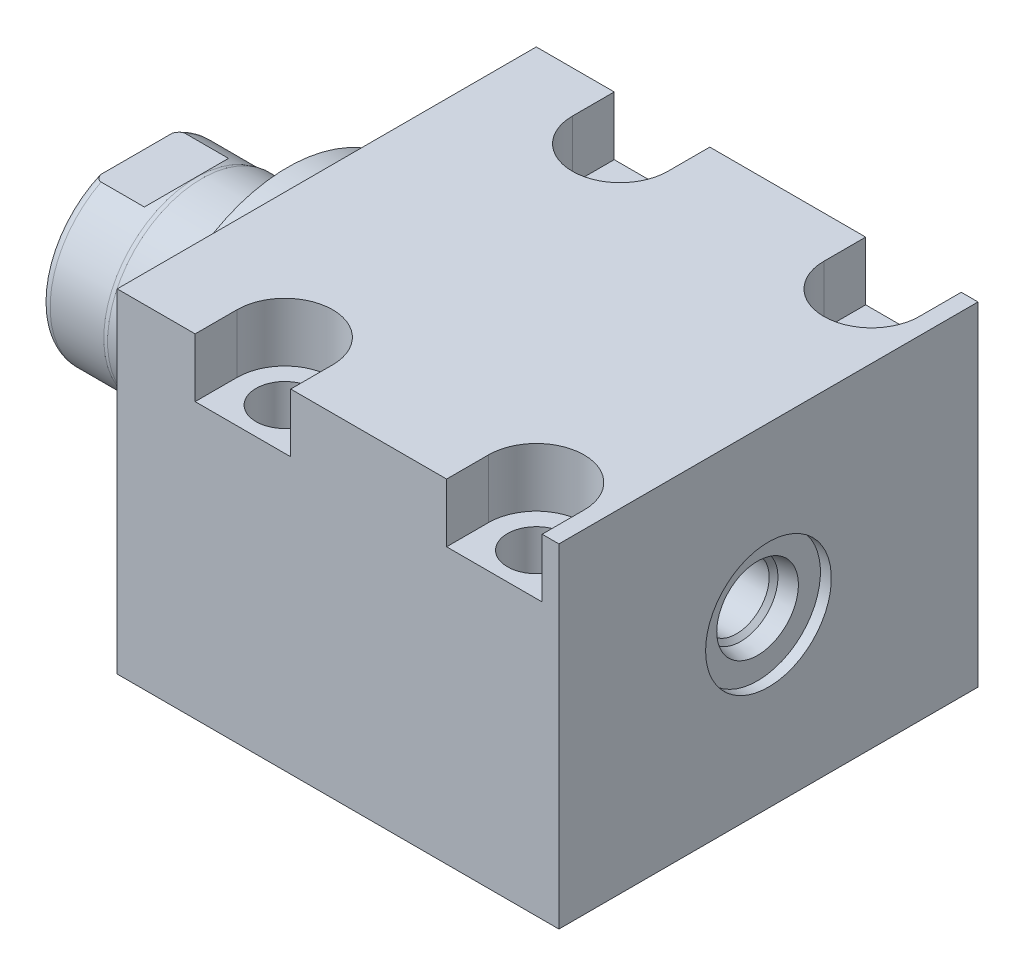
SolidWorks part; units mm, degrees
material "Alloy Steel"
ref_plane "Front Plane" through (0, 0, 0) normal (0, 0, 1) x (1, 0, 0)
ref_plane "Top Plane" through (0, 0, 0) normal (0, 1, 0) x (1, 0, 0)
ref_plane "Right Plane" through (0, 0, 0) normal (1, 0, 0) x (0, 0, -1)
ref_plane "Plane1" through (0, 0, 0) normal (1, 0, 0) x (0, 0, -1)
sketch "Sketch1" plane through (0, 0, 0) normal (1, 0, 0) x (0, 0, -1)
  line L0 (-31.75, 25.146) -> (31.75, 25.146)
  line L1 (31.75, 25.146) -> (31.75, -25.4)
  line L2 (31.75, -25.4) -> (-31.75, -25.4)
  line L3 (-31.75, -25.4) -> (-31.75, 25.146)
  line L4 (0, -24.4475) -> (0, 24.4475) construction
  dimension "D1" = 50.546
  dimension "D2" = 25.4
  dimension "D3" = 63.5
  dimension "D4" = 31.75
extrude "Extrude1" add sketch "Sketch1" along normal blind 66.929
sketch "Sketch5" plane through (0, 0, 0) normal (-1, 0, 0) x (0, 0, 1)
  circle A0 centre (0, 0) radius 22.225
  dimension "D1" = 44.45
extrude "Extrude2" add sketch "Sketch5" along normal blind 5.969
ref_plane "Plane5" through (0, 0, 0) normal (0, -1, 0) x (0, 0, 1)
sketch "Sketch6" plane through (0, 0, 0) normal (0, -1, 0) x (0, 0, 1)
  line L0 (0, 5.969) -> (-14.2875, 5.969)
  line L1 (-14.2875, 5.969) -> (-14.2875, 28.829)
  line L2 (-14.2875, 28.829) -> (0, 28.829)
  line L3 (0, 28.829) -> (0, 5.969)
  line L4 (0, -5.7546) -> (0, 21.1709) construction
  line L5 (22.225, 5.969) -> (-22.225, 5.969) construction
  line L6 (31.75, -66.929) -> (-31.75, -66.929) construction
  dimension "D1" = 95.758
  dimension "D2" = 28.575
revolve "Revolve1" add sketch "Sketch6" angle 360 about L4
ref_plane "Plane6" through (-18.5113, 3.2639, 0) normal (0, 0, 1) x (0, 1, 0)
sketch "S2D0001" plane through (-18.5113, 3.2639, 0) normal (0, 0, 1) x (0, 1, 0)
  line L0 (2.286, 8.25) -> (2.286, -6.5225)
  line L2 (3.4798, 10.3177) -> (-3.2639, 10.3177)
  line L3 (-3.2639, 10.3177) -> (-3.2639, -6.5225)
  line L4 (2.286, 8.25) -> (3.4798, 10.3177)
  line L5 (-3.2639, -18.5113) -> (-3.2639, 2.765) construction
  line L6 (11.0236, 10.3177) -> (-17.5514, 10.3177) construction
  line L7 (2.286, -6.5225) -> (-3.2639, -6.5225)
  dimension "D1" = 30
  dimension "D2" = 13.4874
  dimension "D3" = 11.0998
  dimension "D4" = 16.8402
revolve "Cut-Revolve4" cut sketch "S2D0001" angle 360 about L5
ref_plane "Plane7" through (0, 0, 0) normal (0, 1, 0) x (0, 0, -1)
sketch "Sketch8" plane through (0, 0, 0) normal (0, 1, 0) x (0, 0, -1)
  line L0 (-14.2875, 18.923) -> (-14.097, 19.685)
  line L1 (-14.097, 19.685) -> (-14.097, 27.813)
  line L2 (0, 12.6594) -> (0, 20.8178) construction
  line L3 (-14.2875, 18.923) -> (-14.2875, 28.829)
  line L4 (-13.7089, 28.829) -> (-14.2875, 28.829)
  line L5 (14.2875, 28.829) -> (-14.2875, 28.829) construction
  line L6 (-14.2875, 28.829) -> (-14.2875, 5.969) construction
  arc A0 (-13.7089, 28.829) -> (-14.097, 27.813) centre (-12.573, 27.813) ccw
  dimension "D2" = 1.524
  dimension "D1" = 28.194
  dimension "D3" = 1.016
  dimension "D4" = 0.762
  dimension "D5" = 9.144
revolve "Cut-Revolve5" cut sketch "Sketch8" angle 360 about L2
ref_plane "Plane11" through (0, 0, 0) normal (0, 0, -1) x (0, -1, 0)
sketch "Sketch12" plane through (0, 0, 0) normal (0, 0, -1) x (0, -1, 0)
  line L0 (12.573, 28.829) -> (12.573, 21.2598)
  line L1 (12.573, 21.2598) -> (14.097, 19.7358)
  line L2 (-12.573, 28.829) -> (-12.573, 21.2598)
  line L3 (-12.573, 21.2598) -> (-14.097, 19.7358)
  line L4 (12.573, 28.829) -> (14.097, 28.829)
  line L5 (0, 13.7262) -> (0, 20.767) construction
  line L6 (-14.097, 19.7358) -> (-14.097, 28.829)
  line L8 (14.097, 19.685) -> (14.097, 27.813) construction
  line L9 (14.097, 19.7358) -> (14.097, 28.829)
  line L10 (-12.573, 28.829) -> (-14.097, 28.829)
  line L12 (13.7089, 28.829) -> (-13.7089, 28.829) construction
  dimension "D1" = 25.146
  dimension "D2" = 7.5692
  dimension "D3" = 45
extrude "Cut-Extrude4" cut sketch "Sketch12" against normal mid plane 60.96
hole_wizard "Hole2" positions "Sketch17" profile "Sketch16" legacy
sketch "Sketch17" plane through (0, 25.146, 0) normal (0, 1, 0) x (-1, 0, 0)
  line L0 (0, 0) -> (-59.3363, 0) construction
  line L1 (0, -31.75) -> (0, 31.75) construction
  point P0 (-19.05, -25.4)
  point P9 (-19.05, 25.4)
  dimension "D1" = 50.8
  dimension "D2" = 19.05
sketch "Sketch16" plane through (19.05, 25.146, -25.4) normal (1, 0, 0) x (0, 0, 1)
  line L0 (0, 0) -> (0, 50.546)
  line L1 (0, 50.546) -> (4.3688, 50.546)
  line L2 (4.3688, 50.546) -> (4.3688, 0)
  line L3 (4.3688, 0) -> (0, 0)
  line L4 (0, 110) -> (0, -10) construction
  dimension "Diameter" = 8.7376
  dimension "Depth" = 50.546
pattern_linear "LPattern1" count 2 spacing 38.1 along (1, 0, 0) of "Hole2"
sketch "Sketch18" plane through (0, 25.146, 0) normal (0, 1, 0) x (1, 0, 0)
  line L0 (0, 0) -> (50.053, 0) construction
  line L2 (66.929, -31.75) -> (0, -31.75) construction
  line L4 (64.389, -31.75) -> (49.911, -31.75)
  line L5 (11.811, -25.4) -> (11.811, -31.75)
  line L6 (26.289, -25.4) -> (26.289, -31.75)
  line L7 (49.911, -25.4) -> (49.911, -31.75)
  line L8 (64.389, 25.4) -> (64.389, 31.75)
  line L9 (26.289, -31.75) -> (11.811, -31.75)
  line L12 (26.289, 31.75) -> (11.811, 31.75)
  line L14 (49.911, 25.4) -> (49.911, 31.75)
  line L15 (26.289, 25.4) -> (26.289, 31.75)
  line L16 (11.811, 25.4) -> (11.811, 31.75)
  line L17 (64.389, 31.75) -> (49.911, 31.75)
  line L18 (64.389, -25.4) -> (64.389, -31.75)
  arc A0 (26.289, -25.4) -> (11.811, -25.4) centre (19.05, -25.4) ccw
  arc A1 (64.389, -25.4) -> (49.911, -25.4) centre (57.15, -25.4) ccw
  arc A2 (64.389, 25.4) -> (49.911, 25.4) centre (57.15, 25.4) cw
  arc A3 (26.289, 25.4) -> (11.811, 25.4) centre (19.05, 25.4) cw
  dimension "D1" = 14.478
extrude "Cut-Extrude5" cut sketch "Sketch18" against normal blind 8.89
hole_wizard "Hole3" positions "Sketch20" profile "Sketch19" legacy
sketch "Sketch20" plane through (0, -25.4, 0) normal (0, -1, 0) x (1, 0, 0)
  line L0 (0, 31.75) -> (0, -31.75) construction
  point P0 (12.7, 0)
  dimension "D1" = 12.7
sketch "Sketch19" plane through (12.7, -25.4, 0) normal (1, 0, 0) x (0, 0, -1)
  line L0 (0, 0) -> (0, 10.4789)
  line L1 (0, 10.4789) -> (1.5875, 9.525)
  line L2 (1.5875, 9.525) -> (1.5875, 1.4478)
  line L3 (1.5875, 1.4478) -> (5.6705, 1.4478)
  line L4 (5.6705, 0) -> (0, 0)
  line L5 (0, -11.3109) -> (0, 121.1557) construction
  line L6 (0, 10.4789) -> (-1.5875, 9.525) construction
  line L7 (5.6705, 1.4478) -> (5.6705, 0)
  dimension "Depth" = 9.525
  dimension "Drill Angle" = 118
  dimension "Diameter" = 3.175
  dimension "C-Bore Diameter" = 11.3411
  dimension "C-Bore Depth" = 1.4478
hole_wizard "Hole4" positions "Sketch21" profile "Sketch22" legacy
sketch "Sketch21" plane through (0, -25.4, 0) normal (0, -1, 0) x (1, 0, 0)
  point P0 (50.8, 0)
  dimension "D1" = 38.1
sketch "Sketch22" plane through (50.8, -25.4, 0) normal (1, 0, 0) x (0, 0, -1)
  line L0 (0, 0) -> (0, 10.4789)
  line L1 (0, 10.4789) -> (1.5875, 9.525)
  line L2 (1.5875, 9.525) -> (1.5875, 1.4478)
  line L3 (1.5875, 1.4478) -> (5.6705, 1.4478)
  line L4 (5.6705, 0) -> (0, 0)
  line L5 (0, -11.3109) -> (0, 121.1557) construction
  line L6 (0, 10.4789) -> (-1.5875, 9.525) construction
  line L7 (5.6705, 1.4478) -> (5.6705, 0)
  dimension "Depth" = 9.525
  dimension "Drill Angle" = 118
  dimension "Diameter" = 3.175
  dimension "C-Bore Diameter" = 11.3411
  dimension "C-Bore Depth" = 1.4478
chamfer "Chamfer1" distance 0.635 angle 45 2 edges at (50.8, -23.9522, -1.5875) (12.7, -23.9522, -1.5875)
sketch "Sketch23" plane through (0, 0, 0) normal (0, 0, 1) x (1, 0, 0)
  line L0 (12.7, -23.9522) -> (12.7, -21.4272) construction
  line L1 (10.4775, -23.9522) -> (14.9225, -23.9522) construction
  line L2 (7.0294, -23.9522) -> (18.3705, -23.9522) construction
  line L3 (7.0294, -23.9522) -> (7.0294, -25.4) construction
  circle A0 centre (8.4772, -25.4) radius 1.4478
  dimension "D1" = 2.8956
revolve "Revolve2" add sketch "Sketch23" angle 360 about L0
pattern_linear "LPattern3" count 2 spacing 38.1 along (1, 0, 0) of bodies 128
sketch "Sketch24" plane through (0, 0, 0) normal (0, 0, 1) x (1, 0, 0)
  line L0 (0, 0) -> (74.772, 0) construction
  line L1 (66.929, 9.525) -> (65.278, 9.525)
  line L2 (66.929, 25.146) -> (66.929, -25.4) construction
  line L3 (65.278, 9.525) -> (65.278, 6.1849)
  line L4 (65.278, 6.1849) -> (62.7253, 5.6423)
  line L5 (62.7253, 5.6423) -> (62.0614, 4.9784)
  line L6 (62.0614, 4.9784) -> (50.673, 4.9784)
  line L7 (50.673, 4.9784) -> (50.673, 0)
  line L8 (50.673, 0) -> (66.929, 0)
  line L9 (66.929, 0) -> (66.929, 9.525)
  dimension "D1" = 1.651
  dimension "D2" = 19.05
  dimension "D3" = 9.9568
  dimension "D4" = 16.256
  dimension "D5" = 12
  dimension "D6" = 45
  dimension "D7" = 12.3698
  dimension "D8" = 2.5527
revolve "Cut-Revolve6" cut sketch "Sketch24" angle 360 about L0
